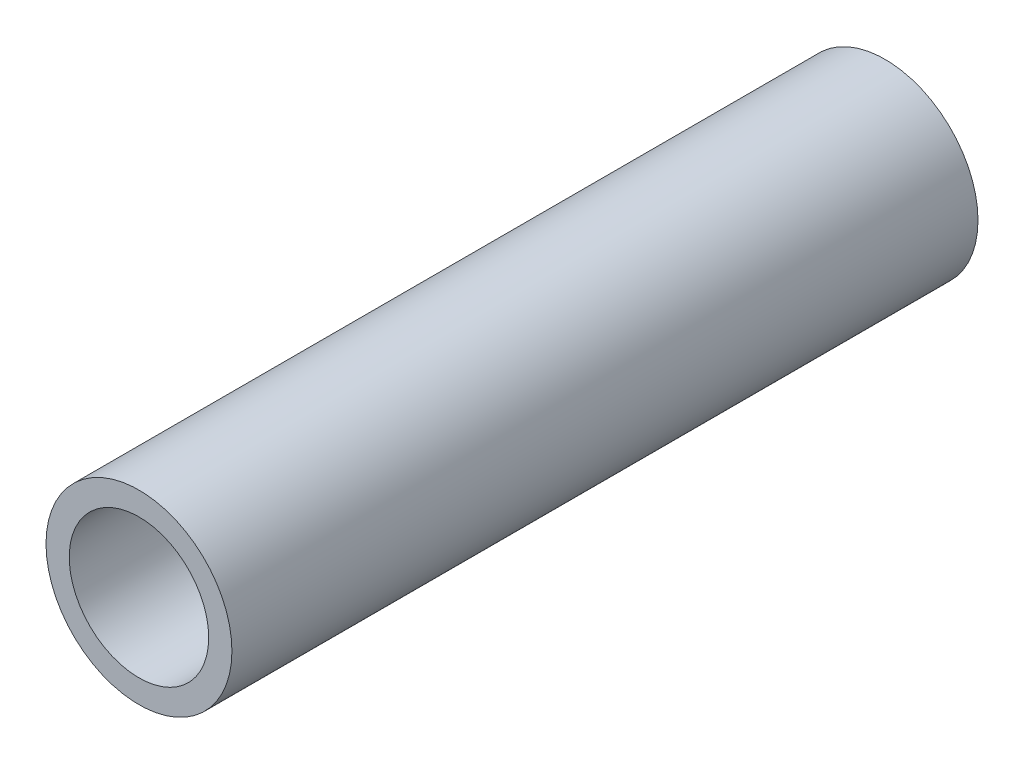
SolidWorks part; units mm, degrees
ref_plane "Front Plane" through (0, 0, 0) normal (0, 0, 1) x (1, 0, 0)
ref_plane "Top Plane" through (0, 0, 0) normal (0, 1, 0) x (1, 0, 0)
ref_plane "Right Plane" through (0, 0, 0) normal (1, 0, 0) x (0, 0, -1)
sketch "Sketch2" plane through (0, 0, 0) normal (0, 0, 1) x (1, 0, 0)
  circle A0 centre (0, 0) radius 3.175
  circle A1 centre (0, 0) radius 4.2333
  dimension "D1" = 6.35
  dimension "D2" = 8.4667
extrude "Boss-Extrude1" add sketch "Sketch2" along normal blind 33.9725
